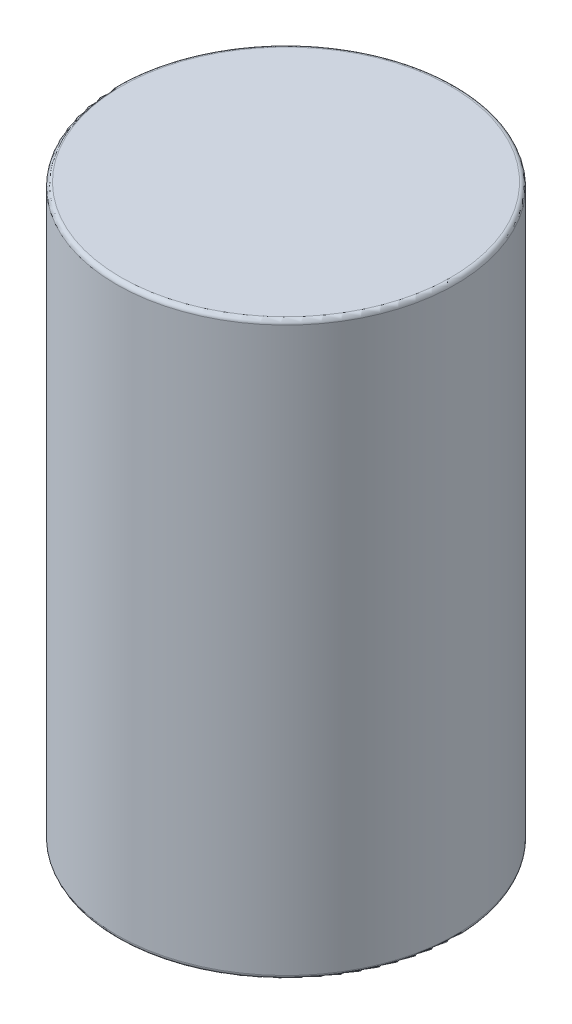
SolidWorks part; units mm, degrees
ref_plane "Спереди" through (0, 0, 0) normal (0, 0, 1) x (1, 0, 0)
ref_plane "Сверху" through (0, 0, 0) normal (0, 1, 0) x (1, 0, 0)
ref_plane "Справа" through (0, 0, 0) normal (1, 0, 0) x (0, 0, -1)
sketch "Эскиз1" plane through (0, 0, 0) normal (0, 1, 0) x (1, 0, 0)
  circle A0 centre (0, 0) radius 4
  dimension "D1" = 8
extrude "Бобышка-Вытянуть1" add sketch "Эскиз1" along normal blind 13.5
fillet "Скругление1" radius 0.1 1 edges at (0, 13.5, 4)
fillet "Скругление2" radius 0.1 1 edges at (0, 0, 4)
